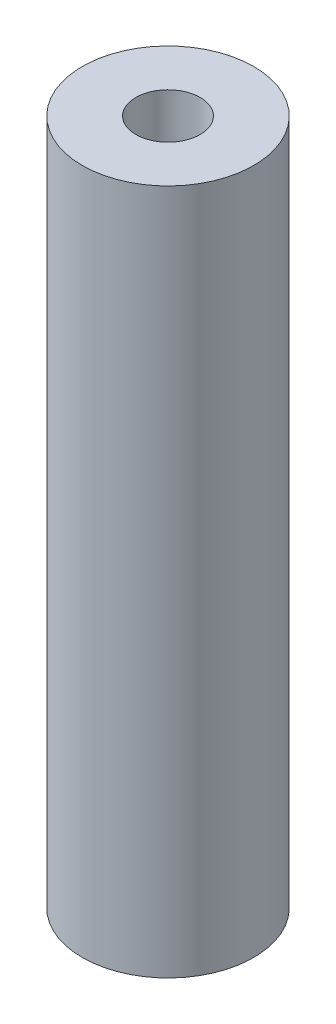
SolidWorks part; units mm, degrees
ref_plane "Front Plane" through (0, 0, 0) normal (0, 0, 1) x (1, 0, 0)
ref_plane "Top Plane" through (0, 0, 0) normal (0, 1, 0) x (1, 0, 0)
ref_plane "Right Plane" through (0, 0, 0) normal (1, 0, 0) x (0, 0, -1)
sketch "Sketch1" plane through (0, 0, 0) normal (0, 1, 0) x (1, 0, 0)
  circle A0 centre (0, 0) radius 4.7625
  circle A1 centre (0, 0) radius 12.7
  dimension "D1" = 9.525
  dimension "D2" = 25.4
extrude "Boss-Extrude1" add sketch "Sketch1" along normal blind 101.6
move or copy body "Body-Move/Copy2" [suppressed] bodies to move or copy 101
move or copy body "Body-Move/Copy1" [suppressed] bodies to move or copy 101
